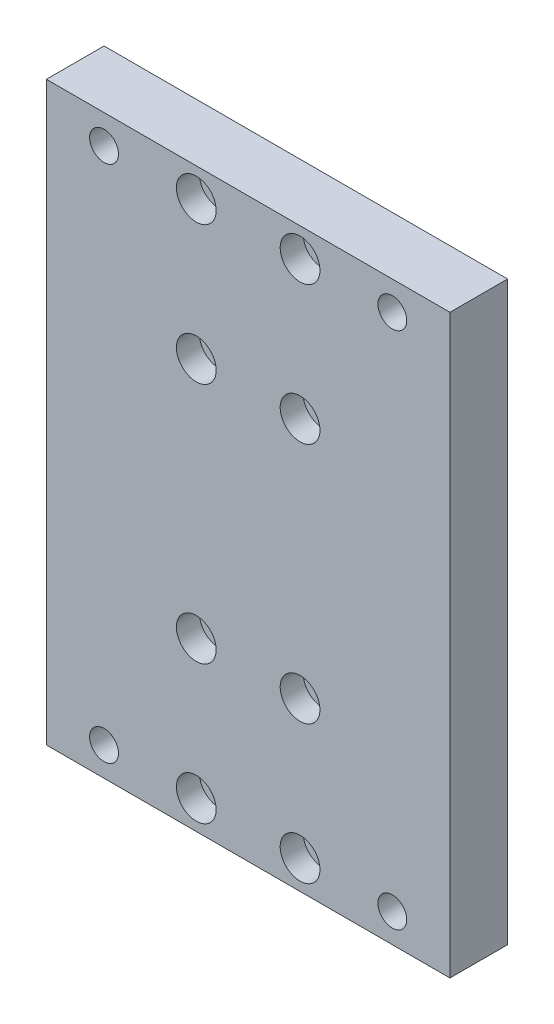
SolidWorks part; units mm, degrees
ref_plane "Front Plane" through (0, 0, 0) normal (0, 0, 1) x (1, 0, 0)
ref_plane "Top Plane" through (0, 0, 0) normal (0, 1, 0) x (1, 0, 0)
ref_plane "Right Plane" through (0, 0, 0) normal (1, 0, 0) x (0, 0, -1)
sketch "Sketch1" plane through (0, 0, 0) normal (0, 0, 1) x (1, 0, 0)
  line L1 (35, -50) -> (-35, -50)
  line L2 (35, -50) -> (35, 50)
  line L3 (35, 50) -> (-35, 50)
  line L4 (-35, -50) -> (-35, 50)
  line L5 (35, -50) -> (-35, 50) construction
  line L6 (35, 50) -> (-35, -50) construction
  point P0 (0, 0)
  dimension "D1" = 70
  dimension "D2" = 100
extrude "Boss-Extrude1" add sketch "Sketch1" along normal blind 10
sketch "Sketch2" plane through (0, 0, 0) normal (0, 0, -1) x (-1, 0, 0)
  line L0 (0, 50) -> (0, 0) construction
  line L1 (-35, 50) -> (35, 50) construction
  line L2 (0, 0) -> (-35, 0) construction
  line L3 (-35, -50) -> (-35, 50) construction
  circle A0 centre (-25, 45) radius 2.5
  circle A1 centre (25, 45) radius 2.5
  circle A2 centre (-25, -45) radius 2.5
  circle A3 centre (25, -45) radius 2.5
  dimension "D1" = 5
  dimension "D2" = 5
  dimension "D3" = 10
extrude "Cut-Extrude1" cut sketch "Sketch2" against normal through all
sketch "Sketch3" plane through (0, 0, 0) normal (0, 0, -1) x (-1, 0, 0)
  circle A1 centre (9, 21) radius 1.5
  circle A2 centre (9, 21) radius 1.5
  circle A3 centre (9, 45) radius 1.5
  circle A4 centre (9, 45) radius 1.5
  circle A5 centre (-9, 21) radius 1.5
  circle A6 centre (-9, 21) radius 1.5
  circle A7 centre (-9, 45) radius 1.5
  circle A8 centre (-9, 45) radius 1.5
  circle A9 centre (9, -45) radius 1.5
  circle A10 centre (9, -45) radius 1.5
  circle A11 centre (9, -21) radius 1.5
  circle A12 centre (9, -21) radius 1.5
  circle A13 centre (-9, -45) radius 1.5
  circle A14 centre (-9, -45) radius 1.5
  circle A15 centre (-9, -21) radius 1.5
  circle A16 centre (-9, -21) radius 1.5
  dimension "D1" = 0
  dimension "D2" = 0
  dimension "D3" = 0
  dimension "D4" = 0
  dimension "D5" = 0
  dimension "D6" = 0
  dimension "D7" = 0
  dimension "D8" = 0
extrude "Cut-Extrude2" cut sketch "Sketch3" against normal through all
sketch "Sketch4" plane through (0, 0, 10) normal (0, 0, 1) x (1, 0, 0)
  line L0 (0, 50) -> (0, 0) construction
  line L1 (35, 50) -> (-35, 50) construction
  line L2 (0, 0) -> (-35, 0) construction
  line L3 (-35, 50) -> (-35, -50) construction
  line L4 (0, 33) -> (-35, 33) construction
  circle A0 centre (-9, 45) radius 3.45
  circle A1 centre (-9, 21) radius 3.45
  circle A2 centre (9, 21) radius 3.45
  circle A3 centre (9, 45) radius 3.45
  circle A4 centre (9, -21) radius 3.45
  circle A5 centre (-9, -21) radius 3.45
  circle A6 centre (-9, -45) radius 3.45
  circle A7 centre (9, -45) radius 3.45
  dimension "D1" = 6.9
extrude "Cut-Extrude3" cut sketch "Sketch4" against normal blind 4
